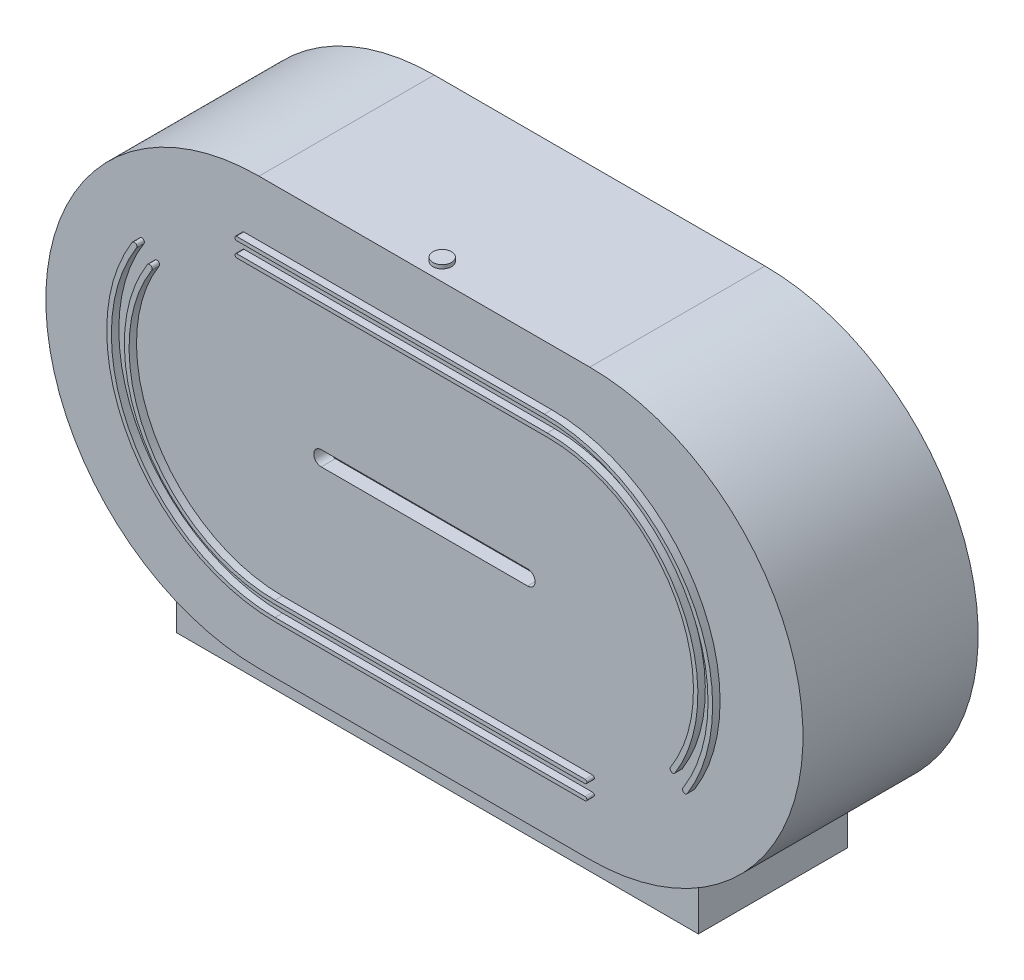
SolidWorks part; units mm, degrees
other "Camera1"
ref_plane "Back wall " through (0, 0, 0) normal (0, 0, 1) x (1, 0, 0)
ref_plane "Top Plane" through (0, 0, 0) normal (0, 1, 0) x (1, 0, 0)
ref_plane "Right Plane" through (0, 0, 0) normal (1, 0, 0) x (0, 0, -1)
sketch "Sketch1" plane through (0, 0, 0) normal (0, 0, 1) x (1, 0, 0)
  line L0 (-76.2854, 56.8005) -> (149.1396, 56.8005)
  line L5 (-76.2854, -233.7755) -> (149.1396, -233.7755)
  arc A0 (-76.2854, 56.8005) -> (-76.2854, -233.7755) centre (-76.2854, -88.4875) ccw
  arc A1 (149.1396, 56.8005) -> (149.1396, -233.7755) centre (149.1396, -88.4875) cw
  dimension "D2" = 145.288
  dimension "D1" = 225.425
extrude "Boss-Extrude1" add sketch "Sketch1" along normal blind 119.38
ref_plane "Plane1" through (0, -249.6505, 0) normal (0, -1, 0) x (-1, 0, 0)
sketch "Sketch2" plane through (0, -249.6505, 0) normal (0, -1, 0) x (-1, 0, 0)
  line L0 (-36.4271, 0) -> (-36.4271, -119.38) construction
  line L1 (76.2854, 0) -> (-149.1396, 0) construction
  line L2 (76.2854, -119.38) -> (-149.1396, -119.38) construction
  line L3 (-214.2271, -110.49) -> (141.3729, -110.49)
  line L4 (141.3729, -110.49) -> (141.3729, -8.89)
  line L5 (141.3729, -8.89) -> (-214.2271, -8.89)
  line L6 (76.2854, -119.38) -> (221.5734, -119.38) construction
  line L7 (221.5734, 0) -> (76.2854, 0) construction
  line L8 (-214.2271, -110.49) -> (-214.2271, -8.89)
  point P15 (-36.4271, -8.89)
  point P16 (-36.4271, -110.49)
  dimension "D1" = 8.89
  dimension "D2" = 8.89
  dimension "D3" = 177.8
extrude "Boss-Extrude2" add sketch "Sketch2" against normal blind 44.958
ref_plane "Floor" through (0, -757.6505, 0) normal (0, -1, 0) x (-1, 0, 0)
sketch "Sketch3" plane through (0, 0, 119.38) normal (0, 0, 1) x (1, 0, 0)
  line L0 (36.4271, 56.8005) -> (36.4271, -233.7755) construction
  line L1 (149.1396, 56.8005) -> (-76.2854, 56.8005) construction
  line L2 (-76.2854, -233.7755) -> (149.1396, -233.7755) construction
  line L3 (294.4276, -88.4875) -> (-221.5734, -88.4875) construction
  line L4 (-33.8952, -83.4075) -> (106.7493, -83.4075)
  line L5 (-33.8952, -93.5675) -> (106.7493, -93.5675)
  arc A0 (149.1396, -233.7755) -> (149.1396, 56.8005) centre (149.1396, -88.4875) ccw construction
  arc A1 (-76.2854, 56.8005) -> (-76.2854, -233.7755) centre (-76.2854, -88.4875) ccw construction
  arc A2 (-33.8952, -83.4075) -> (-33.8952, -93.5675) centre (-33.8952, -88.4875) ccw
  arc A3 (106.7493, -83.4075) -> (106.7493, -93.5675) centre (106.7493, -88.4875) cw
  point P17 (36.4271, -83.4075)
  point P22 (36.4271, -93.5675)
  dimension "D1" = 5.08
extrude "Cut-Extrude1" cut sketch "Sketch3" against normal blind 9.652
sketch "Sketch4" plane through (0, 56.8005, 0) normal (0, 1, 0) x (1, 0, 0)
  line L1 (36.4271, -119.38) -> (36.4271, 0) construction
  line L2 (149.1396, -119.38) -> (-76.2854, -119.38) construction
  line L3 (-297.8363, 0) -> (297.8363, 0) construction
  circle A1 centre (36.4271, -107.2284) radius 6.35
  dimension "D1" = 12.7
extrude "Boss-Extrude3" add sketch "Sketch4" along normal blind 2.54
sketch "Sketch5" plane through (0, 0, 119.38) normal (0, 0, 1) x (1, 0, 0)
  line L0 (-174.3637, 18.7005) -> (229.5716, -209.4804) construction
  line L1 (-86.4791, 18.7005) -> (123.2511, 18.7005)
  line L2 (-86.4791, 16.1605) -> (123.2511, 16.1605)
  line L3 (-86.3134, 8.5405) -> (125.1937, 8.5405)
  line L4 (-86.3134, 6.0005) -> (125.6086, 6.0005)
  line L5 (32.6682, 56.8005) -> (32.6682, -233.7755) construction
  line L6 (149.1396, 56.8005) -> (-76.2854, 56.8005) construction
  line L7 (-76.2854, -233.7755) -> (149.1396, -233.7755) construction
  line L8 (150.9621, -185.5155) -> (-60.2958, -185.5155)
  line L9 (150.9621, -195.6755) -> (-60.2958, -195.6755)
  line L10 (150.9621, -182.9755) -> (-60.2958, -182.9755)
  line L11 (150.9621, -193.1355) -> (-60.2958, -193.1355)
  line L12 (-76.2854, -233.7755) -> (149.1396, -233.7755) construction
  arc A0 (-76.2854, 56.8005) -> (-76.2854, -233.7755) centre (-76.2854, -88.4875) ccw construction
  arc A1 (149.1396, -233.7755) -> (149.1396, 56.8005) centre (149.1396, -88.4875) ccw construction
  arc A2 (-86.4791, 16.1605) -> (-86.4791, 18.7005) centre (-86.4791, 17.4305) cw
  arc A3 (-86.3134, 6.0005) -> (-86.3134, 8.5405) centre (-86.3134, 7.2705) cw
  arc A4 (123.2511, 18.7005) -> (220.6126, -156.5809) centre (123.2511, -95.9803) cw
  arc A5 (123.2511, 16.1605) -> (217.8939, -154.3985) centre (123.2511, -95.3775) cw
  arc A6 (125.1937, 8.5405) -> (212.2304, -148.6228) centre (125.1937, -94.1415) cw
  arc A7 (125.6086, 6.0005) -> (209.2196, -146.7306) centre (125.6086, -93.251) cw
  arc A8 (209.2196, -146.7306) -> (212.2304, -148.6228) centre (210.7175, -147.6887) ccw
  arc A9 (220.6126, -156.5809) -> (217.8939, -154.3985) centre (219.122, -155.6531) cw
  arc A10 (-144.3178, -30.2382) -> (-147.3325, -28.3521) centre (-145.8196, -29.2863) ccw
  arc A11 (-60.2958, -193.1355) -> (-154.9386, -22.5765) centre (-60.2958, -81.5975) cw
  arc A12 (-60.2958, -195.6755) -> (-157.6573, -20.3941) centre (-60.2958, -80.9947) cw
  arc A13 (150.9621, -193.1355) -> (150.9621, -195.6755) centre (150.9621, -194.4055) cw
  arc A14 (-60.2958, -182.9755) -> (-144.3178, -30.2382) centre (-60.2958, -83.4963) cw
  arc A15 (-157.6573, -20.3941) -> (-154.9386, -22.5765) centre (-156.1667, -21.3218) cw
  arc A16 (150.9621, -182.9755) -> (150.9621, -185.5155) centre (150.9621, -184.2455) cw
  arc A17 (-60.2958, -185.5155) -> (-147.3325, -28.3521) centre (-60.2958, -82.8335) cw
  dimension "D3" = 3.556
  dimension "D1" = 2.54
  dimension "D2" = 2.54
  dimension "D4" = 3.4863
  dimension "D5" = 38.1
  dimension "D6" = 7.62
  dimension "D7" = 38.1
  dimension "D8" = 7.62
  dimension "D9" = 92.9405
  dimension "D10" = 92.964
  dimension "D11" = 92.964
  dimension "D12" = 92.964
  dimension "D13" = 92.964
extrude "Boss-Extrude4" add sketch "Sketch5" along normal blind 5.08
